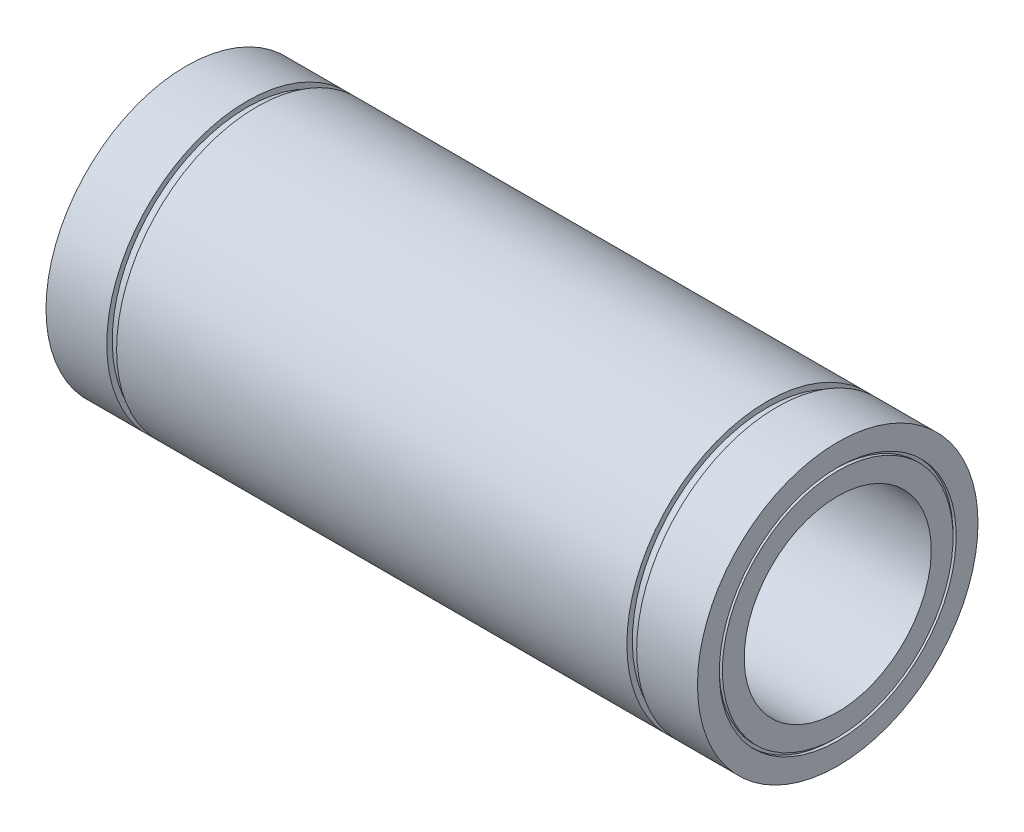
SolidWorks part; units mm, degrees
material "Ст3сп ГОСТ 535-2005"
ref_plane "Plano frontal" through (0, 0, 0) normal (0, 0, 1) x (1, 0, 0)
ref_plane "Plano superior" through (0, 0, 0) normal (0, 1, 0) x (1, 0, 0)
ref_plane "Plano direito" through (0, 0, 0) normal (1, 0, 0) x (0, 0, -1)
sketch "Esboço1" plane through (0, 0, 0) normal (0, 0, 1) x (1, 0, 0)
  line L0 (-104.5, 45) -> (-85, 45)
  line L1 (-85, 45) -> (-85, 43.25)
  line L2 (-85, 43.25) -> (-81.85, 43.25)
  line L3 (-81.85, 43.25) -> (-81.85, 45)
  line L4 (-81.85, 45) -> (81.85, 45)
  line L5 (81.85, 45) -> (81.85, 43.25)
  line L6 (81.85, 43.25) -> (85, 43.25)
  line L7 (85, 43.25) -> (85, 45)
  line L8 (85, 45) -> (104.5, 45)
  line L9 (104.5, 45) -> (104.5, 38)
  line L10 (104.5, 30) -> (-104.5, 30)
  line L11 (-104.5, 30) -> (-104.5, 37)
  line L12 (0, 30) -> (0, 0) construction
  line L13 (0, 0) -> (-86.5, 0) construction
  line L14 (-104.5, 38) -> (-104.5, 45)
  line L15 (-104.5, 38) -> (-103.5, 38)
  line L16 (104.5, 37) -> (104.5, 30)
  line L17 (-103.5, 38) -> (-103.5, 37)
  line L18 (-103.5, 37) -> (-104.5, 37)
  line L19 (104.5, 38) -> (103.5, 38)
  line L21 (104.5, 37) -> (103.5, 37)
  line L22 (103.5, 38) -> (103.5, 37)
  dimension "D1" = 209
  dimension "D2" = 170
  dimension "D3" = 3.15
  dimension "D4" = 60
  dimension "D5" = 90
  dimension "D6" = 86.5
  dimension "D7" = 1
  dimension "D8" = 1
  dimension "D9" = 1
  dimension "D10" = 1
revolve "Revolução1" add sketch "Esboço1" angle 360 about L13
